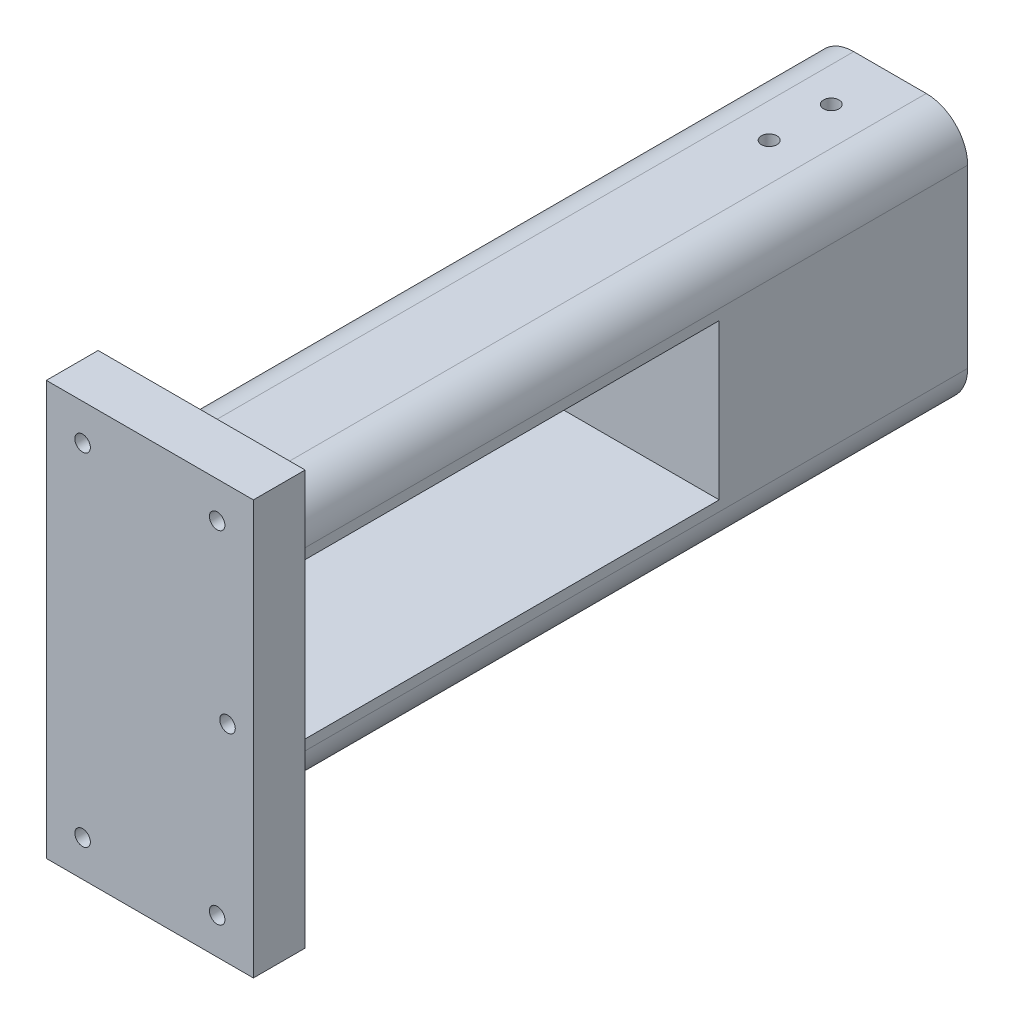
SolidWorks part; units mm, degrees
ref_plane "Front Plane" through (0, 0, 0) normal (0, 0, 1) x (1, 0, 0)
ref_plane "Top Plane" through (0, 0, 0) normal (0, 1, 0) x (1, 0, 0)
ref_plane "Right Plane" through (0, 0, 0) normal (1, 0, 0) x (0, 0, -1)
sketch "Sketch1" plane through (0, 0, 0) normal (0, 0, 1) x (1, 0, 0)
  line L1 (12.0012, 45.4242) -> (-27.9988, 45.4242)
  line L2 (12.0012, 45.4242) -> (12.0012, -34.5758)
  line L3 (12.0012, -34.5758) -> (-27.9988, -34.5758)
  line L4 (-27.9988, 45.4242) -> (-27.9988, -34.5758)
  dimension "D1" = 80
  dimension "D2" = 40
extrude "Boss-Extrude1" add sketch "Sketch1" along normal blind 10
sketch "Sketch2" plane through (0, 0, 0) normal (0, 0, -1) x (-1, 0, 0)
  line L0 (27.9988, 45.4242) -> (27.9988, -34.5758) construction
  line L1 (-2.0012, -19.5758) -> (27.9988, -19.5758)
  line L2 (-2.0012, -19.5758) -> (-2.0012, 30.4242)
  line L3 (-2.0012, 30.4242) -> (27.9988, 30.4242)
  line L4 (27.9988, -19.5758) -> (27.9988, 30.4242)
  line L5 (27.9988, -34.5758) -> (-12.0012, -34.5758) construction
  dimension "D1" = 0
  dimension "D2" = 50
  dimension "D3" = 15
  dimension "D4" = 30
extrude "Boss-Extrude2" add sketch "Sketch2" along normal blind 100
sketch "Sketch4" plane through (-27.9988, 0, 0) normal (-1, 0, 0) x (0, 0, 1)
  line L0 (-100, -19.5758) -> (0, -19.5758) construction
  line L1 (-90, -9.5758) -> (-10, -9.5758)
  line L2 (-90, -9.5758) -> (-90, 20.4242)
  line L3 (-90, 20.4242) -> (-10, 20.4242)
  line L4 (-10, -9.5758) -> (-10, 20.4242)
  line L5 (-100, 30.4242) -> (0, 30.4242) construction
  line L6 (-100, -19.5758) -> (-100, 30.4242) construction
  line L7 (0, 45.4242) -> (0, 30.4242) construction
  dimension "D1" = 10
  dimension "D2" = 10
  dimension "D3" = 10
  dimension "D4" = 10
extrude "Cut-Extrude1" cut sketch "Sketch4" against normal blind 150
sketch "Sketch3" plane through (0, 0, -100) normal (0, 0, -1) x (-1, 0, 0)
  line L1 (20.9988, 20.4242) -> (5.6988, 20.4242)
  line L2 (20.9988, 20.4242) -> (20.9988, -10.0758)
  line L3 (20.9988, -10.0758) -> (5.6988, -10.0758)
  line L4 (5.6988, 20.4242) -> (5.6988, -10.0758)
  line L5 (27.9988, 30.4242) -> (-2.0012, 30.4242) construction
  line L6 (27.9988, -19.5758) -> (27.9988, 30.4242) construction
  line L7 (-2.0012, -19.5758) -> (27.9988, -19.5758) construction
  line L8 (-2.0012, -19.5758) -> (27.9988, -19.5758)
  line L11 (-2.0012, -19.5758) -> (-2.0012, 30.4242)
  line L12 (-2.0012, 30.4242) -> (27.9988, 30.4242)
  line L13 (27.9988, -19.5758) -> (27.9988, 30.4242)
  line L14 (-2.0012, 30.4242) -> (-2.0012, -19.5758) construction
  dimension "D1" = 10
  dimension "D2" = 7
  dimension "D3" = 0
  dimension "D4" = 0
  dimension "D5" = 30.5
  dimension "D6" = 15.3
  dimension "D7" = 0
  dimension "D8" = 0
extrude "Boss-Extrude3" add sketch "Sketch3" along normal blind 38
fillet "Fillet1" radius 8 2 edges at (2.0012, -19.5758, -69)
fillet "Fillet2" radius 8 1 edges at (2.0012, 30.4242, -69)
fillet "Fillet3" radius 8 1 edges
fillet "Fillet4" radius 8 2 edges
sketch "Sketch5" plane through (0, 20.4242, 0) normal (0, -1, 0) x (1, 0, 0)
  line L0 (-20.9988, -100) -> (-5.6988, -100) construction
  line L1 (-5.6988, -138) -> (-5.6988, -100) construction
  circle A0 centre (-13.3488, -115) radius 1.5
  circle A1 centre (-13.3488, -127) radius 1.5
  dimension "D1" = 3
  dimension "D2" = 3
  dimension "D3" = 15
  dimension "D4" = 7.65
  dimension "D5" = 27
  dimension "D6" = 7.65
extrude "Cut-Extrude2" cut sketch "Sketch5" against normal through all both and the other way through all
sketch "Sketch6" plane through (0, 0, 0) normal (0, 0, -1) x (-1, 0, 0)
  line L0 (27.9988, -34.5758) -> (-12.0012, -34.5758) construction
  line L1 (27.9988, -11.5758) -> (27.9988, -34.5758) construction
  line L2 (-12.0012, -34.5758) -> (-12.0012, 45.4242) construction
  line L3 (27.9988, 45.4242) -> (27.9988, 22.4242) construction
  line L4 (-12.0012, 45.4242) -> (27.9988, 45.4242) construction
  circle A0 centre (20.9988, 38.4242) radius 1.5
  circle A2 centre (-5.0012, 38.4242) radius 1.5
  circle A3 centre (20.9988, -27.5758) radius 1.5
  circle A5 centre (-5.0012, -27.5758) radius 1.5
  circle A6 centre (-7.0012, 5.4242) radius 1.5
  dimension "D1" = 3
  dimension "D2" = 7
  dimension "D3" = 3
  dimension "D4" = 3
  dimension "D5" = 3
  dimension "D6" = 3
  dimension "D7" = 7
  dimension "D8" = 7
  dimension "D9" = 7
  dimension "D10" = 7
  dimension "D11" = 7
  dimension "D12" = 7
  dimension "D13" = 7
  dimension "D14" = 5
  dimension "D15" = 40
extrude "Cut-Extrude3" cut sketch "Sketch6" against normal blind 40
